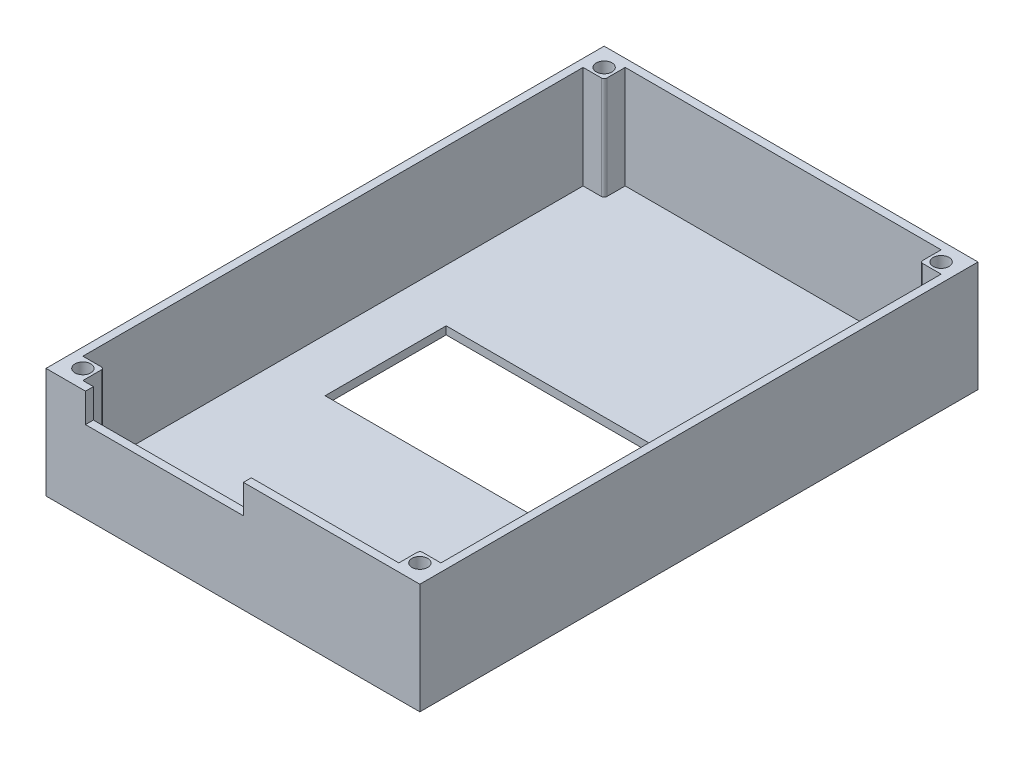
SolidWorks part; units mm, degrees
ref_plane "Front Plane" through (0, 0, 0) normal (0, 0, 1) x (1, 0, 0)
ref_plane "Top Plane" through (0, 0, 0) normal (0, 1, 0) x (1, 0, 0)
ref_plane "Right Plane" through (0, 0, 0) normal (1, 0, 0) x (0, 0, -1)
sketch "Sketch2" plane through (0, 0, 0) normal (0, 1, 0) x (1, 0, 0)
  line L1 (-35.5, -53) -> (35.5, -53)
  line L2 (-35.5, -53) -> (-35.5, 53)
  line L3 (-35.5, 53) -> (35.5, 53)
  line L4 (35.5, -53) -> (35.5, 53)
  line L5 (-35.5, -53) -> (35.5, 53) construction
  line L6 (-35.5, 53) -> (35.5, -53) construction
  point P0 (0, 0)
  dimension "D1" = 106
  dimension "D2" = 71
extrude "Boss-Extrude1" add sketch "Sketch2" along normal blind 21
shell "Shell1" thickness 1.5
sketch "Sketch3" plane through (0, 0, 53) normal (0, 0, 1) x (1, 0, 0)
  line L0 (-35.5, 21) -> (35.5, 21) construction
  line L1 (-28, 21) -> (2, 21)
  line L2 (-28, 21) -> (-28, 15.5)
  line L3 (-28, 15.5) -> (2, 15.5)
  line L4 (2, 21) -> (2, 15.5)
  dimension "D1" = 2
  dimension "D2" = 30
  dimension "D3" = 5.5
extrude "Cut-Extrude1" cut sketch "Sketch3" against normal blind 21
sketch "Sketch4" plane through (0, 1.5, 0) normal (0, 1, 0) x (1, 0, 0)
  line L6 (-32, 49.5) -> (-32, 51.5) construction
  line L7 (-34, 51.5) -> (-30, 51.5)
  line L8 (-34, 51.5) -> (-34, 47.5)
  line L9 (-34, 47.5) -> (-30.5, 47.5)
  line L10 (-30, 51.5) -> (-30, 48)
  line L11 (-32, 49.5) -> (-34, 49.5) construction
  circle A0 centre (-32, 49.5) radius 1.5
  arc A2 (-30.5, 47.5) -> (-30, 48) centre (-30.5, 48) ccw
  dimension "D2" = 3
  dimension "D1" = 4
  dimension "D3" = 0.5
extrude "Boss-Extrude2" add sketch "Sketch4" along normal up to surface (19.5 mm away) up to face at (-4.3333, 21, 17.4167)
ref_plane "Plane1" through (0, 0, 0) normal (-1, 0, 0) x (0, 0, 1)
ref_plane "Plane2" through (0, 0, 0) normal (0, 0, -1) x (-1, 0, 0)
mirror "Mirror1" about plane through (0, 0, 0) normal (-1, 0, 0) of "Boss-Extrude2" second plane through (0, 0, 0) second plane normal (0, 0, -1)
sketch "Sketch5" plane through (0, 1.5, 0) normal (0, 1, 0) x (1, 0, 0)
  line L0 (-34, 47.5) -> (-34, -47.5) construction
  line L1 (24, -11.5) -> (-24, -11.5)
  line L2 (24, -11.5) -> (24, 11.5)
  line L3 (24, 11.5) -> (-24, 11.5)
  line L4 (-24, -11.5) -> (-24, 11.5)
  line L5 (24, -11.5) -> (-24, 11.5) construction
  line L6 (24, 11.5) -> (-24, -11.5) construction
  line L7 (-30, -51.5) -> (30, -51.5) construction
  point P0 (0, 0)
  dimension "D1" = 10
  dimension "D2" = 40
extrude "Cut-Extrude2" cut sketch "Sketch5" against normal blind 1.5
